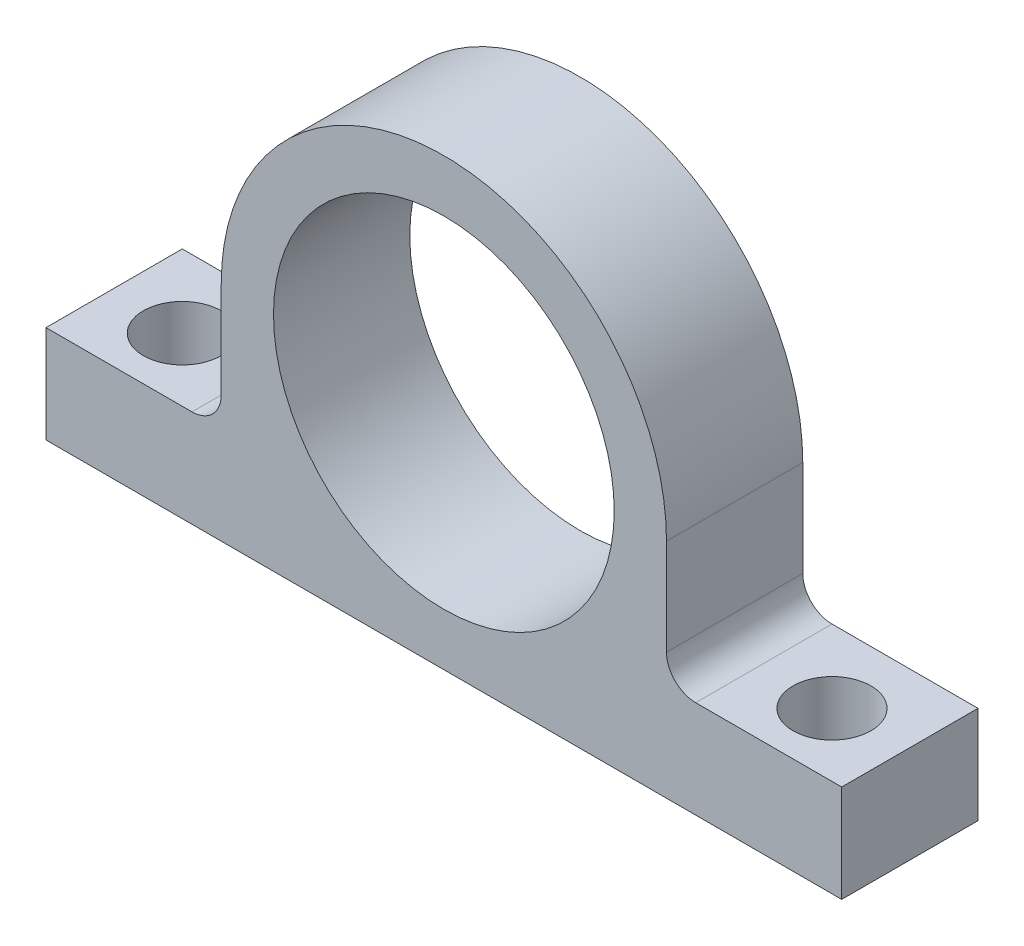
SolidWorks part; units mm, degrees
ref_plane "Front Plane" through (0, 0, 0) normal (0, 0, 1) x (1, 0, 0)
ref_plane "Top Plane" through (0, 0, 0) normal (0, 1, 0) x (1, 0, 0)
ref_plane "Right Plane" through (0, 0, 0) normal (1, 0, 0) x (0, 0, -1)
sketch "Sketch1" plane through (0, 0, 0) normal (0, 0, 1) x (1, 0, 0)
  line L0 (0, 0) -> (0, -22.87) construction
  line L1 (40.87, -22.87) -> (-40.87, -22.87)
  line L2 (-40.87, -22.87) -> (-40.87, -12.87)
  line L3 (-22.87, 0) -> (-22.87, -9.87)
  line L4 (-25.87, -12.87) -> (-40.87, -12.87)
  line L5 (25.87, -12.87) -> (40.87, -12.87)
  line L6 (40.87, -22.87) -> (40.87, -12.87)
  line L7 (22.87, 0) -> (22.87, -9.87)
  circle A0 centre (0, 0) radius 17.5
  arc A1 (22.87, 0) -> (-22.87, 0) centre (0, 0) ccw
  arc A2 (-25.87, -12.87) -> (-22.87, -9.87) centre (-25.87, -9.87) ccw
  arc A3 (25.87, -12.87) -> (22.87, -9.87) centre (25.87, -9.87) cw
  dimension "D1" = 3
extrude "Boss-Extrude1" add sketch "Sketch1" along normal blind 14
sketch "Sketch2" plane through (0, -12.87, 0) normal (0, 1, 0) x (1, 0, 0)
  circle A0 centre (33.37, -7.5) radius 4
extrude "Cut-Extrude1" cut sketch "Sketch2" against normal through all
mirror "Mirror1" about plane through (0, 0, 0) normal (1, 0, 0) of "Cut-Extrude1"
